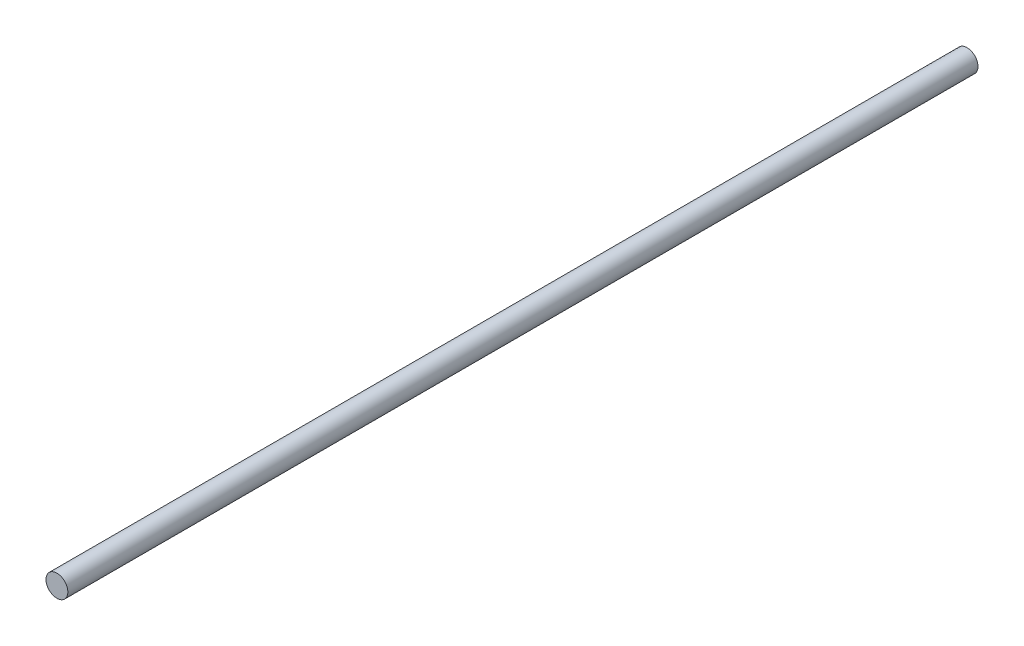
SolidWorks part; units mm, degrees
ref_plane "Front Plane" through (0, 0, 0) normal (0, 0, 1) x (1, 0, 0)
ref_plane "Top Plane" through (0, 0, 0) normal (0, 1, 0) x (1, 0, 0)
ref_plane "Right Plane" through (0, 0, 0) normal (1, 0, 0) x (0, 0, -1)
sketch "Sketch1" plane through (0, 0, 0) normal (0, 0, 1) x (1, 0, 0)
  circle A0 centre (0, 0) radius 6
extrude "Boss-Extrude1" add sketch "Sketch1" along normal blind 500
